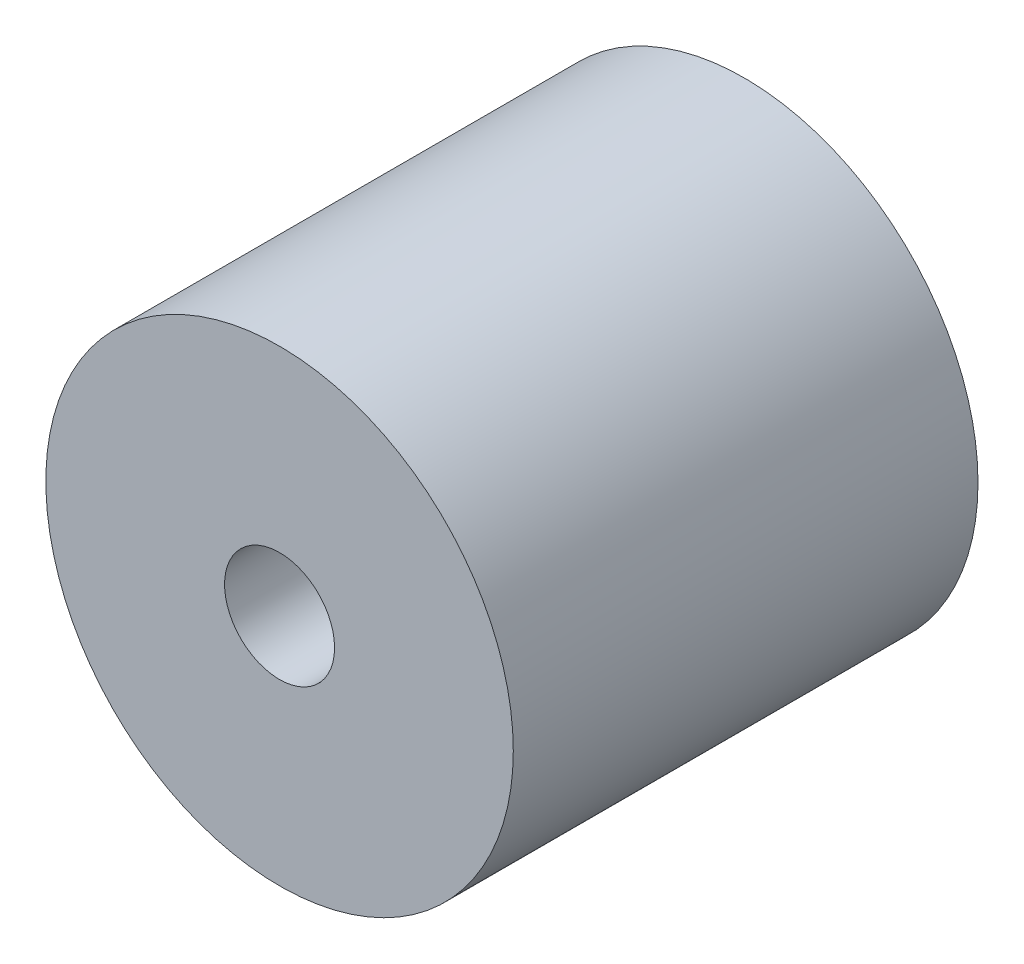
SolidWorks part; units mm, degrees
material "Rubber"
ref_plane "Front Plane" through (0, 0, 0) normal (0, 0, 1) x (1, 0, 0)
ref_plane "Top Plane" through (0, 0, 0) normal (0, 1, 0) x (1, 0, 0)
ref_plane "Right Plane" through (0, 0, 0) normal (1, 0, 0) x (0, 0, -1)
sketch "Sketch1" plane through (0, 0, 0) normal (0, 0, 1) x (1, 0, 0)
  circle A0 centre (0, 0) radius 2.125
  circle A1 centre (0, 0) radius 0.5
  dimension "D1" = 4.25
  dimension "D2" = 1
extrude "Boss-Extrude1" add sketch "Sketch1" along normal blind 4.225
